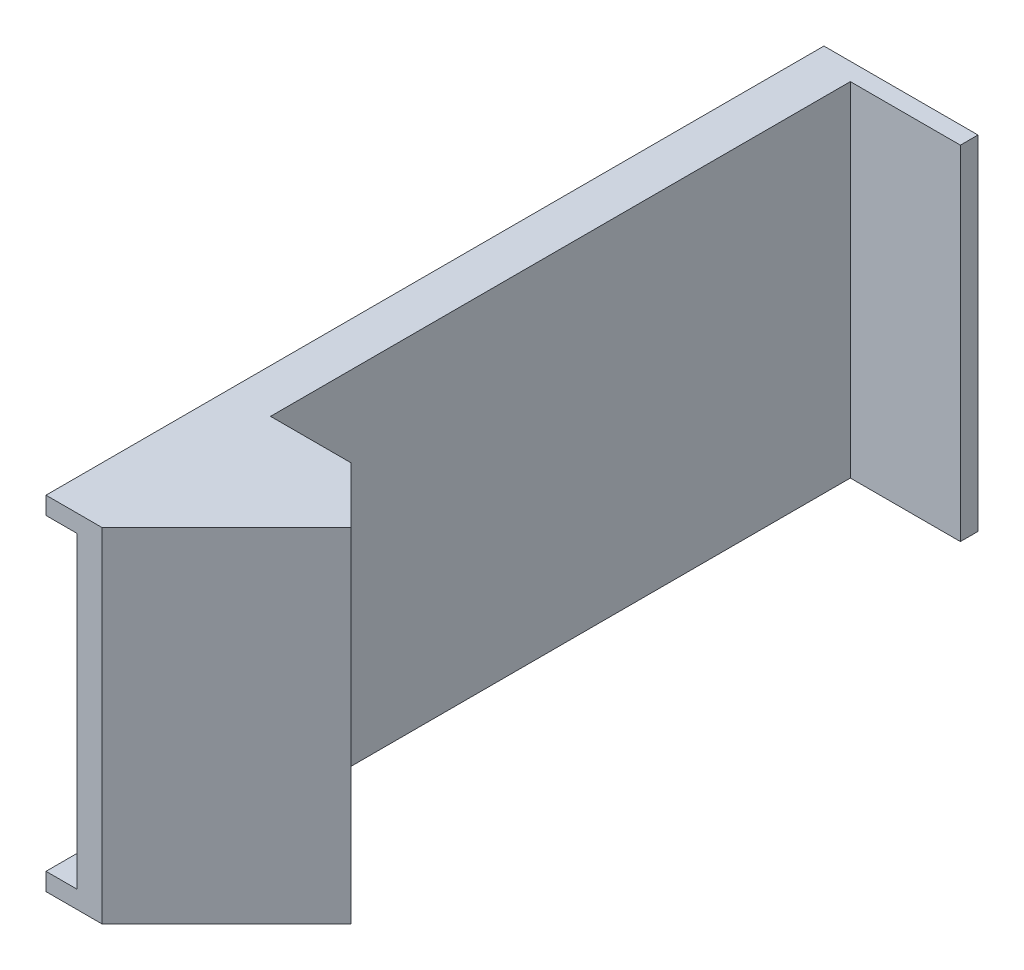
SolidWorks part; units mm, degrees
ref_plane "Front Plane" through (0, 0, 0) normal (0, 0, 1) x (1, 0, 0)
ref_plane "Top Plane" through (0, 0, 0) normal (0, 1, 0) x (1, 0, 0)
ref_plane "Right Plane" through (0, 0, 0) normal (1, 0, 0) x (0, 0, -1)
sketch "Sketch1" plane through (0, 0, 0) normal (0, 0, 1) x (1, 0, 0)
  line L1 (-15, -19.5) -> (15, -19.5)
  line L2 (-15, -19.5) -> (-15, 19.5)
  line L3 (-15, 19.5) -> (15, 19.5)
  line L4 (15, -19.5) -> (15, 19.5)
  line L5 (-15, -19.5) -> (15, 19.5) construction
  line L6 (-15, 19.5) -> (15, -19.5) construction
  point P0 (0, 0)
  dimension "D1" = 30
  dimension "D2" = 39
extrude "Boss-Extrude1" add sketch "Sketch1" along normal blind 2
sketch "Sketch2" plane through (0, 0, 2) normal (0, 0, 1) x (1, 0, 0)
  line L0 (15, 19.5) -> (-15, 19.5) construction
  line L1 (-2.5, 19.5) -> (2.5, 19.5)
  line L2 (-2.5, 19.5) -> (-2.5, -19.5)
  line L3 (-2.5, -19.5) -> (2.5, -19.5)
  line L4 (2.5, 19.5) -> (2.5, -19.5)
  line L5 (-15, -19.5) -> (15, -19.5) construction
  dimension "D1" = 5
  dimension "D2" = 12.5
extrude "Boss-Extrude2" add sketch "Sketch2" along normal blind 80
sketch "Sketch3" plane through (0, -19.5, 0) normal (0, -1, 0) x (1, 0, 0)
  line L0 (-2.5, 82) -> (2.5, 82)
  line L1 (2.5, 82) -> (2.5, 77)
  line L2 (2.5, 82) -> (2.5, 2) construction
  line L3 (2.5, 77) -> (-2.5, 82)
  dimension "D1" = 5
extrude "Cut-Extrude1" cut sketch "Sketch3" against normal blind 39
sketch "Sketch4" plane through (39.75, 0, 39.75) normal (0.7071, 0, 0.7071) x (0.7071, 0, -0.7071)
  line L1 (-59.7505, 19.5) -> (-39.7505, 19.5)
  line L2 (-59.7505, 19.5) -> (-59.7505, -19.5)
  line L3 (-59.7505, -19.5) -> (-39.7505, -19.5)
  line L4 (-39.7505, 19.5) -> (-39.7505, -19.5)
  dimension "D1" = 20
extrude "Boss-Extrude3" add sketch "Sketch4" along normal blind 9
sketch "Sketch5" plane through (-28.1079, 0, 28.1079) normal (0.7071, 0, -0.7071) x (-0.7071, 0, -0.7071)
  line L0 (-65.215, 19.5) -> (-56.215, 19.5) construction
  line L1 (-63.215, 17.5) -> (-58.215, 17.5)
  line L2 (-63.215, 17.5) -> (-63.215, -17.5)
  line L3 (-63.215, -17.5) -> (-58.215, -17.5)
  line L4 (-58.215, 17.5) -> (-58.215, -17.5)
  line L5 (-65.215, -19.5) -> (-65.215, 19.5) construction
  line L6 (-56.215, 19.5) -> (-56.215, -19.5) construction
  line L7 (-65.215, -19.5) -> (-56.215, -19.5) construction
  dimension "D1" = 2
  dimension "D2" = 2
  dimension "D3" = 2
  dimension "D4" = 2
extrude "Cut-Extrude2" cut sketch "Sketch5" against normal blind 30
sketch "Sketch6" plane through (0, 0, 2) normal (0, 0, 1) x (1, 0, 0)
  line L1 (-2.5, 19.5) -> (-15, 19.5)
  line L2 (-2.5, 19.5) -> (-2.5, -19.5)
  line L3 (-2.5, -19.5) -> (-15, -19.5)
  line L4 (-15, 19.5) -> (-15, -19.5)
extrude "Cut-Extrude3" cut sketch "Sketch6" against normal blind 2
sketch "Sketch7" plane through (0, -19.5, 0) normal (0, -1, 0) x (1, 0, 0)
  line L0 (-2.5, 82) -> (3.864, 88.364)
  line L1 (3.864, 88.364) -> (-2.5, 88.364)
  line L2 (-2.5, 88.364) -> (-2.5, 82)
extrude "Boss-Extrude4" add sketch "Sketch7" against normal blind 39
sketch "Sketch8" plane through (0, -19.5, 0) normal (0, -1, 0) x (1, 0, 0)
  line L0 (2.5, 77) -> (11.6421, 67.8579)
  line L1 (11.6421, 67.8579) -> (2.5, 67.8579)
  line L2 (2.5, 77) -> (2.5, 2) construction
  line L3 (2.5, 67.8579) -> (2.5, 77)
extrude "Boss-Extrude5" add sketch "Sketch8" against normal blind 39
sketch "Sketch10" plane through (-42.25, 0, 42.25) normal (0.7071, 0, -0.7071) x (-0.7071, 0, -0.7071)
  line L1 (-63.215, -17.5) -> (-58.215, -17.5)
  line L2 (-63.215, -17.5) -> (-63.215, 17.5)
  line L3 (-63.215, 17.5) -> (-58.215, 17.5)
  line L4 (-58.215, -17.5) -> (-58.215, 17.5)
extrude "Cut-Extrude4" cut sketch "Sketch10" against normal blind 10
